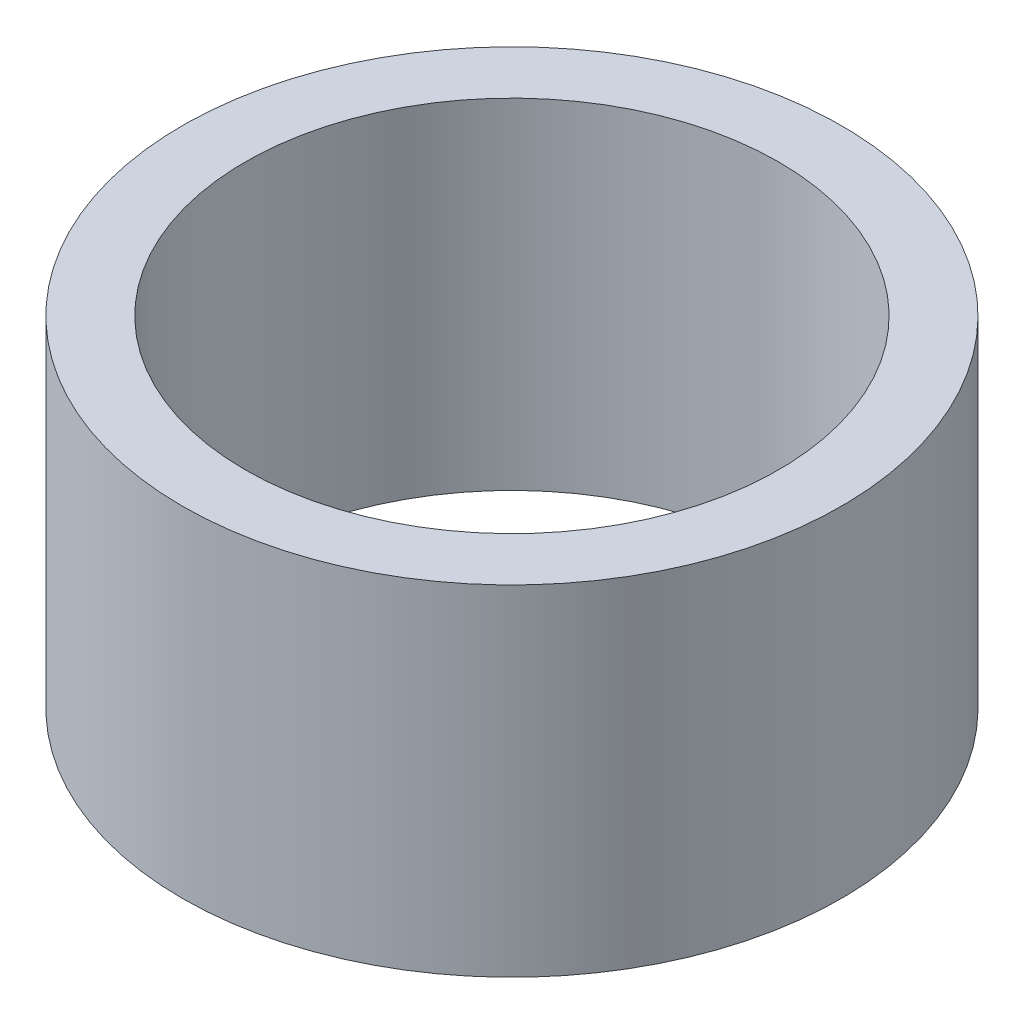
SolidWorks part; units mm, degrees
ref_plane "前视基准面" through (0, 0, 0) normal (0, 0, 1) x (1, 0, 0)
ref_plane "上视基准面" through (0, 0, 0) normal (0, 1, 0) x (1, 0, 0)
ref_plane "右视基准面" through (0, 0, 0) normal (1, 0, 0) x (0, 0, -1)
sketch "草图1" plane through (0, 0, 0) normal (0, 1, 0) x (1, 0, 0)
  circle A0 centre (0, 0) radius 3.925
  circle A1 centre (0, 0) radius 4.85
  dimension "D1" = 7.85
  dimension "D2" = 9.7
  dimension "D3" = 0.925
extrude "凸台-拉伸1" add sketch "草图1" along normal blind 5
